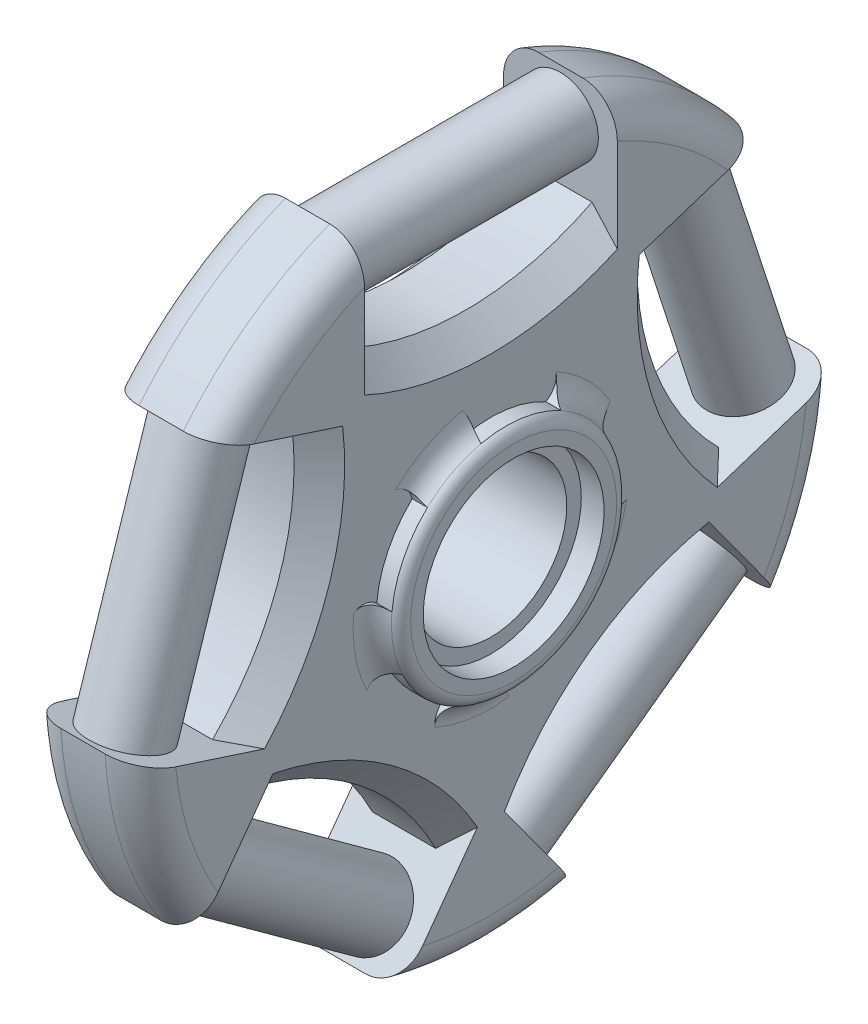
SolidWorks part; units mm, degrees
ref_plane "Front Plane" through (0, 0, 0) normal (0, 0, 1) x (1, 0, 0)
ref_plane "Top Plane" through (0, 0, 0) normal (0, 1, 0) x (1, 0, 0)
ref_plane "Right Plane" through (0, 0, 0) normal (1, 0, 0) x (0, 0, -1)
sketch "Sketch1" plane through (0, 0, 0) normal (1, 0, 0) x (0, 0, -1)
  line L0 (32.8598, 21.1914) -> (13.8386, 15.0111)
  line L1 (-10, 37.8) -> (10, 37.8)
  line L2 (-10, 37.8) -> (-10, 17.8)
  line L4 (10, 37.8) -> (10, 17.8)
  line L5 (-10, 37.8) -> (10, 17.8) construction
  line L6 (-10, 17.8) -> (10, 37.8) construction
  line L7 (39.0401, 2.1703) -> (20.019, -4.0101)
  line L8 (32.8598, 21.1914) -> (39.0401, 2.1703)
  line L9 (30.3085, -24.703) -> (18.5527, -8.5226)
  line L10 (14.1281, -36.4587) -> (2.3724, -20.2784)
  line L11 (30.3085, -24.703) -> (14.1281, -36.4587)
  line L12 (-14.1281, -36.4587) -> (-2.3724, -20.2784)
  line L13 (-30.3085, -24.703) -> (-18.5527, -8.5226)
  line L14 (-14.1281, -36.4587) -> (-30.3085, -24.703)
  line L15 (-39.0401, 2.1703) -> (-20.019, -4.0101)
  line L16 (-32.8598, 21.1914) -> (-13.8386, 15.0111)
  line L17 (-39.0401, 2.1703) -> (-32.8598, 21.1914)
  circle A0 centre (0, 0) radius 27.8
  arc A1 (-10, 17.8) -> (10, 17.8) centre (0, 37.3959) ccw
  arc A2 (13.8386, 15.0111) -> (20.019, -4.0101) centre (35.5656, 11.556) ccw
  arc A3 (18.5527, -8.5226) -> (2.3724, -20.2784) centre (21.9808, -30.2539) ccw
  arc A4 (-2.3724, -20.2784) -> (-18.5527, -8.5226) centre (-21.9808, -30.2539) ccw
  arc A5 (-20.019, -4.0101) -> (-13.8386, 15.0111) centre (-35.5656, 11.556) ccw
  circle A6 centre (0, 0) radius 6
  point P3 (0, 27.8)
  point P31 (0, 0)
  dimension "D1" = 55.6
  dimension "D4" = 22
  dimension "D6" = 12
  dimension "D2" = 20
  dimension "D3" = 20
  dimension "D5" = 5
extrude "Boss-Extrude2" add sketch "Sketch1" along normal blind 9 contours A5 L15 A0 L13 A4 L12 L10 A3 L9 L7 A2 L0 L4 A1 L2 L16 A6
fillet "Fillet1" radius 2.75 10 edges at (0, -8.5907, 26.4394) (9, -8.5907, 26.4394) (9, -27.8, 0) (0, -27.8, 0) (9, -8.5907, -26.4394) (0, -8.5907, -26.4394) (0, 22.4907, -16.3404) (9, 22.4907, -16.3404) (9, 22.4907, 16.3404) (0, 22.4907, 16.3404)
sketch "Sketch3" plane through (0, 0, 0) normal (-1, 0, 0) x (0, 0, 1)
  circle A0 centre (0, 0) radius 7.15
  circle A1 centre (0, 0) radius 9.15
  dimension "D1" = 14.3
  dimension "D2" = 18.3
extrude "Boss-Extrude3" add sketch "Sketch3" along normal blind 1.8 and the other way blind 10.8
chamfer "Chamfer2" distance 2 angle 45 10 edges at (9, -12.4556, -9.0495) (9, 4.7576, -14.6424) (9, -12.4556, 9.0495) (9, 4.7576, 14.6424) (9, 15.3959, 0) (0, 4.7576, 14.6424) (0, -12.4556, 9.0495) (0, -12.4556, -9.0495) (0, 4.7576, -14.6424) (0, 15.3959, 0)
fillet "Fillet3" radius 1 2 edges at (10.8, 0, 9.15) (-1.8, 0, 9.15)
fillet "Fillet4" radius 2 2 edges at (0, 0, -9.15) (9, 0, -9.15)
sketch "Sketch5" plane through (0, 0, 0) normal (-1, 0, 0) x (0, 0, 1)
  line L0 (6.2981, -6.5219) -> (7.5715, -7.8405) construction
  line L1 (0, 0) -> (4.168, -4.316) construction
  line L2 (0, 0) -> (6, 0) construction
  arc A0 (9.8091, -4.7521) -> (4.4069, -9.9689) centre (0, 0) cw
  circle A1 centre (0, 0) radius 10.8995 construction
  arc A2 (8.1947, -3.8793) -> (3.5909, -8.3251) centre (0, 0) cw
  circle A3 centre (0, 0) radius 9.0665 construction
  arc A4 (3.5909, -8.3251) -> (4.4069, -9.9689) centre (2.8248, -9.7298) cw
  arc A5 (8.1947, -3.8793) -> (9.8091, -4.7521) centre (8.3785, -5.4687) cw
  circle A6 centre (0, 0) radius 6 construction
  arc A7 (-1.1571, -8.9924) -> (-1.4883, -10.7975) centre (-2.6119, -9.6583) cw
  arc A8 (-1.4883, -10.7975) -> (-8.1192, -7.2717) centre (0, 0) cw
  arc A9 (-6.808, -5.9878) -> (-8.1192, -7.2717) centre (-8.3806, -5.6932) cw
  arc A10 (-1.1571, -8.9924) -> (-6.808, -5.9878) centre (0, 0) cw
  arc A11 (-8.9098, -1.6783) -> (-10.7289, -1.9211) centre (-9.9928, -0.5005) cw
  arc A12 (-10.7289, -1.9211) -> (-9.4248, 5.4747) centre (0, 0) cw
  arc A13 (-7.7985, 4.6244) -> (-9.4248, 5.4747) centre (-8.0044, 6.2111) cw
  arc A14 (-8.9098, -1.6783) -> (-7.7985, 4.6244) centre (0, 0) cw
  arc A15 (-4.3495, 7.9551) -> (-5.1425, 9.6101) centre (-3.5639, 9.349) cw
  arc A16 (-5.1425, 9.6101) -> (2.2944, 10.6553) centre (0, 0) cw
  arc A17 (1.9882, 8.8458) -> (2.2944, 10.6553) centre (3.4337, 9.5319) cw
  arc A18 (-4.3495, 7.9551) -> (1.9882, 8.8458) centre (0, 0) cw
  arc A19 (6.2217, 6.5949) -> (7.5507, 7.8605) centre (7.7901, 6.2785) cw
  arc A20 (7.5507, 7.8605) -> (10.8428, 1.1106) centre (0, 0) cw
  arc A21 (9.0273, 0.8426) -> (10.8428, 1.1106) centre (10.1265, -0.3201) cw
  arc A22 (6.2217, 6.5949) -> (9.0273, 0.8426) centre (0, 0) cw
  point P45 (0, 0)
  dimension "D2" = 1.6
  dimension "D1" = 46
  dimension "D3" = 7
  dimension "D4" = 6.4
  dimension "D5" = 5
extrude "Cut-Extrude1" cut sketch "Sketch5" along normal blind 1.8
ref_plane "Plane2" through (4.5, 0, 0) normal (1, 0, 0) x (0, 0, -1)
mirror "Mirror1" about plane through (4.5, 0, 0) normal (1, 0, 0) of "Cut-Extrude1"
sketch "Sketch6" plane through (0, -5.8779, -8.0902) normal (0, 0.5878, 0.809) x (1, 0, 0)
  line L3 (6.25, -25.9392) -> (2.75, -25.9392) construction
  line L4 (9, -22.9674) -> (9, -15.5785) construction
  circle A0 centre (4.5, -22.4392) radius 3
  dimension "D1" = 6
  dimension "D2" = 3.5
  dimension "D3" = 4.5
extrude "Boss-Extrude4" add sketch "Sketch6" along normal up to surface (120.6544 mm away)
sketch "Sketch7" plane through (0, -9.5106, 3.0902) normal (0, 0.9511, -0.309) x (1, 0, 0)
  line L1 (6.25, -25.9392) -> (2.75, -25.9392) construction
  line L2 (0, -22.9674) -> (0, -15.5785) construction
  circle A0 centre (4.5, -22.4392) radius 3
  dimension "D1" = 6
  dimension "D2" = 3.5
  dimension "D3" = 4.5
extrude "Boss-Extrude5" add sketch "Sketch7" along normal up to surface (16.122 mm away)
sketch "Sketch8" plane through (0, 0, -10) normal (0, 0, 1) x (1, 0, 0)
  line L0 (9, 22.9674) -> (9, 15.5785) construction
  line L1 (6.25, 25.9392) -> (2.75, 25.9392) construction
  circle A0 centre (4.5, 22.4392) radius 3
  dimension "D1" = 6
  dimension "D2" = 4.5
  dimension "D3" = 3.5
extrude "Boss-Extrude6" add sketch "Sketch8" along normal up to surface (20 mm away) contours A0 up to face at (4.6972, 20.7476, 10)
sketch "Sketch9" plane through (0, -5.8779, 8.0902) normal (0, 0.5878, -0.809) x (-1, 0, 0)
  line L0 (-6.25, -25.9392) -> (-2.75, -25.9392) construction
  line L1 (-9, -22.9674) -> (-9, -15.5785) construction
  circle A0 centre (-4.5, -22.4392) radius 3
  dimension "D1" = 6
  dimension "D2" = 3.5
  dimension "D3" = 4.5
extrude "Boss-Extrude7" add sketch "Sketch9" along normal up to surface (20 mm away) up to face at (4.6972, -10.9073, -20.2853)
sketch "Sketch10" plane through (0, -9.5106, -3.0902) normal (0, 0.9511, 0.309) x (1, 0, 0)
  line L1 (6.25, 25.9392) -> (2.75, 25.9392) construction
  line L2 (9, 22.9674) -> (9, 15.5785) construction
  circle A0 centre (4.5, 22.4392) radius 3
  dimension "D1" = 6
  dimension "D2" = 3.5
  dimension "D3" = 4.5
extrude "Boss-Extrude8" add sketch "Sketch10" along normal up to surface (20 mm away) up to face at (4.6972, 15.9219, -16.6419)
